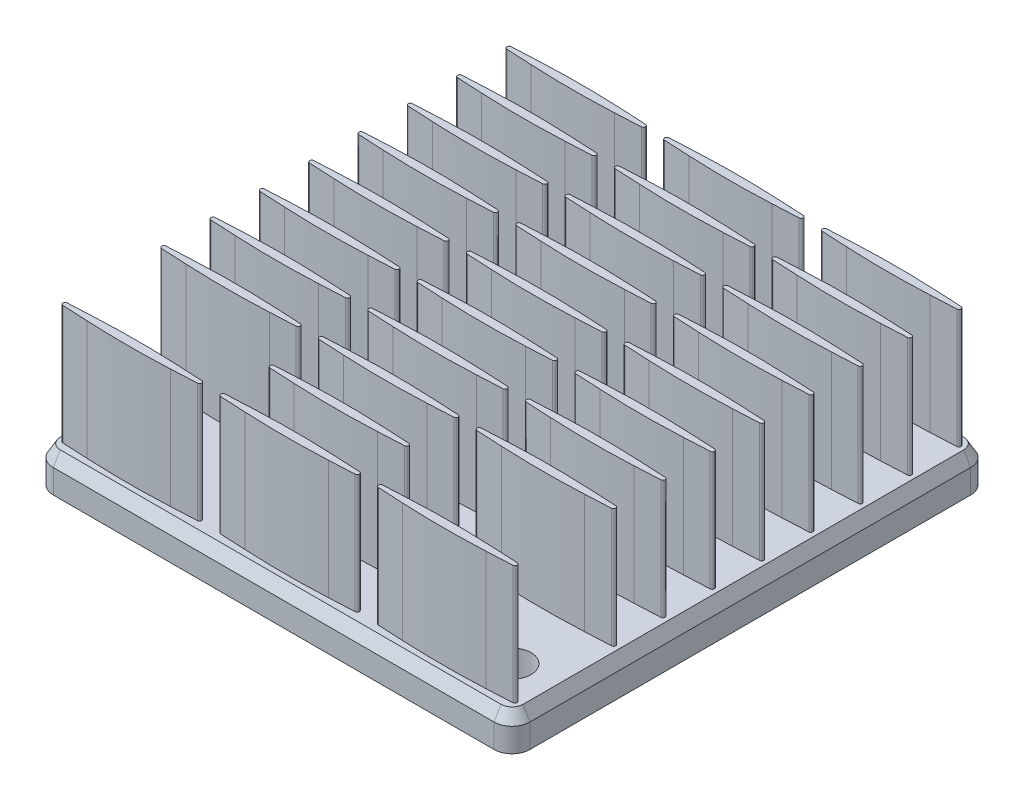
SolidWorks part; units mm, degrees
material "6061 Alloy"
ref_plane "Front Plane" through (0, 0, 0) normal (0, 0, 1) x (1, 0, 0)
ref_plane "Top Plane" through (0, 0, 0) normal (0, 1, 0) x (1, 0, 0)
ref_plane "Right Plane" through (0, 0, 0) normal (1, 0, 0) x (0, 0, -1)
ref_plane "Plane1" through (0, 3, 0) normal (0, 1, 0) x (1, 0, 0)
sketch "Sketch1" plane through (0, 3, 0) normal (0, 1, 0) x (1, 0, 0)
  line L0 (-19.4226, 18.5) -> (-19.4226, -18.5)
  line L1 (-18.5, -19.4226) -> (18.5, -19.4226)
  line L2 (19.4226, -18.5) -> (19.4226, 18.5)
  line L3 (18.5, 19.4226) -> (-18.5, 19.4226)
  arc A0 (-19.4226, -18.5) -> (-18.5, -19.4226) centre (-18.5, -18.5) ccw
  arc A1 (18.5, -19.4226) -> (19.4226, -18.5) centre (18.5, -18.5) ccw
  arc A2 (19.4226, 18.5) -> (18.5, 19.4226) centre (18.5, 18.5) ccw
  arc A3 (-18.5, 19.4226) -> (-19.4226, 18.5) centre (-18.5, 18.5) ccw
extrude "Boss-Extrude1" add sketch "Sketch1" against normal blind 1 draft 30 draft outward yes
sketch "Sketch2" plane through (0, 2, 0) normal (0, -1, 0) x (1, 0, 0)
  line L0 (-20, -18.5) -> (-20, 18.5)
  line L1 (-18.5, 20) -> (18.5, 20)
  line L2 (20, 18.5) -> (20, -18.5)
  line L3 (18.5, -20) -> (-18.5, -20)
  arc A0 (-18.5, -20) -> (-20, -18.5) centre (-18.5, -18.5) cw
  arc A1 (-20, 18.5) -> (-18.5, 20) centre (-18.5, 18.5) cw
  arc A2 (18.5, 20) -> (20, 18.5) centre (18.5, 18.5) cw
  arc A3 (20, -18.5) -> (18.5, -20) centre (18.5, -18.5) cw
extrude "Boss-Extrude2" add sketch "Sketch2" along normal blind 2
sketch "Sketch3" plane through (0, 3, 0) normal (0, 1, 0) x (-1, 0, 0)
  line L0 (-16.7428, -18.9173) -> (-18.889, -18.8098)
  line L1 (-18.889, -18.4502) -> (-16.7428, -18.3427)
  line L2 (-9.7372, -18.3427) -> (-7.591, -18.4502)
  line L3 (-7.591, -18.8098) -> (-9.7372, -18.9173)
  arc A0 (-9.7372, -18.9173) -> (-16.7428, -18.9173) centre (-13.24, 50.995) cw
  arc A1 (-18.889, -18.8098) -> (-18.889, -18.4502) centre (-18.88, -18.63) cw
  arc A2 (-16.7428, -18.3427) -> (-9.7372, -18.3427) centre (-13.24, -88.255) cw
  arc A3 (-7.591, -18.4502) -> (-7.591, -18.8098) centre (-7.6, -18.63) cw
extrude "Boss-Extrude3" add sketch "Sketch3" along normal blind 10
sketch "Sketch4" plane through (0, 3, 0) normal (0, 1, 0) x (-1, 0, 0)
  line L0 (-3.5028, -18.9173) -> (-5.649, -18.8098)
  line L1 (-5.649, -18.4502) -> (-3.5028, -18.3427)
  line L2 (3.5028, -18.3427) -> (5.649, -18.4502)
  line L3 (5.649, -18.8098) -> (3.5028, -18.9173)
  arc A0 (3.5028, -18.9173) -> (-3.5028, -18.9173) centre (0, 50.995) cw
  arc A1 (-5.649, -18.8098) -> (-5.649, -18.4502) centre (-5.64, -18.63) cw
  arc A2 (-3.5028, -18.3427) -> (3.5028, -18.3427) centre (0, -88.255) cw
  arc A3 (5.649, -18.4502) -> (5.649, -18.8098) centre (5.64, -18.63) cw
extrude "Boss-Extrude4" add sketch "Sketch4" along normal blind 12
sketch "Sketch5" plane through (0, 3, 0) normal (0, 1, 0) x (-1, 0, 0)
  line L0 (9.7372, -18.9173) -> (7.591, -18.8098)
  line L1 (7.591, -18.4502) -> (9.7372, -18.3427)
  line L2 (16.7428, -18.3427) -> (18.889, -18.4502)
  line L3 (18.889, -18.8098) -> (16.7428, -18.9173)
  arc A0 (16.7428, -18.9173) -> (9.7372, -18.9173) centre (13.24, 50.995) cw
  arc A1 (7.591, -18.8098) -> (7.591, -18.4502) centre (7.6, -18.63) cw
  arc A2 (9.7372, -18.3427) -> (16.7428, -18.3427) centre (13.24, -88.255) cw
  arc A3 (18.889, -18.4502) -> (18.889, -18.8098) centre (18.88, -18.63) cw
extrude "Boss-Extrude5" add sketch "Sketch5" along normal blind 12
sketch "Sketch6" plane through (0, 3, 0) normal (0, 1, 0) x (-1, 0, 0)
  line L0 (-16.7428, -14.7773) -> (-18.889, -14.6698)
  line L1 (-18.889, -14.3102) -> (-16.7428, -14.2027)
  line L2 (-9.7372, -14.2027) -> (-7.591, -14.3102)
  line L3 (-7.591, -14.6698) -> (-9.7372, -14.7773)
  arc A0 (-9.7372, -14.7773) -> (-16.7428, -14.7773) centre (-13.24, 55.135) cw
  arc A1 (-18.889, -14.6698) -> (-18.889, -14.3102) centre (-18.88, -14.49) cw
  arc A2 (-16.7428, -14.2027) -> (-9.7372, -14.2027) centre (-13.24, -84.115) cw
  arc A3 (-7.591, -14.3102) -> (-7.591, -14.6698) centre (-7.6, -14.49) cw
extrude "Boss-Extrude6" add sketch "Sketch6" along normal blind 12
sketch "Sketch7" plane through (0, 3, 0) normal (0, 1, 0) x (-1, 0, 0)
  line L0 (-3.5028, -14.7773) -> (-5.649, -14.6698)
  line L1 (-5.649, -14.3102) -> (-3.5028, -14.2027)
  line L2 (3.5028, -14.2027) -> (5.649, -14.3102)
  line L3 (5.649, -14.6698) -> (3.5028, -14.7773)
  arc A0 (3.5028, -14.7773) -> (-3.5028, -14.7773) centre (0, 55.135) cw
  arc A1 (-5.649, -14.6698) -> (-5.649, -14.3102) centre (-5.64, -14.49) cw
  arc A2 (-3.5028, -14.2027) -> (3.5028, -14.2027) centre (0, -84.115) cw
  arc A3 (5.649, -14.3102) -> (5.649, -14.6698) centre (5.64, -14.49) cw
extrude "Boss-Extrude7" add sketch "Sketch7" along normal blind 12
sketch "Sketch8" plane through (0, 3, 0) normal (0, 1, 0) x (-1, 0, 0)
  line L0 (9.7372, -14.7773) -> (7.591, -14.6698)
  line L1 (7.591, -14.3102) -> (9.7372, -14.2027)
  line L2 (16.7428, -14.2027) -> (18.889, -14.3102)
  line L3 (18.889, -14.6698) -> (16.7428, -14.7773)
  arc A0 (16.7428, -14.7773) -> (9.7372, -14.7773) centre (13.24, 55.135) cw
  arc A1 (7.591, -14.6698) -> (7.591, -14.3102) centre (7.6, -14.49) cw
  arc A2 (9.7372, -14.2027) -> (16.7428, -14.2027) centre (13.24, -84.115) cw
  arc A3 (18.889, -14.3102) -> (18.889, -14.6698) centre (18.88, -14.49) cw
extrude "Boss-Extrude8" add sketch "Sketch8" along normal blind 12
sketch "Sketch9" plane through (0, 3, 0) normal (0, 1, 0) x (-1, 0, 0)
  line L0 (-16.7428, -10.6373) -> (-18.889, -10.5298)
  line L1 (-18.889, -10.1702) -> (-16.7428, -10.0627)
  line L2 (-9.7372, -10.0627) -> (-7.591, -10.1702)
  line L3 (-7.591, -10.5298) -> (-9.7372, -10.6373)
  arc A0 (-9.7372, -10.6373) -> (-16.7428, -10.6373) centre (-13.24, 59.275) cw
  arc A1 (-18.889, -10.5298) -> (-18.889, -10.1702) centre (-18.88, -10.35) cw
  arc A2 (-16.7428, -10.0627) -> (-9.7372, -10.0627) centre (-13.24, -79.975) cw
  arc A3 (-7.591, -10.1702) -> (-7.591, -10.5298) centre (-7.6, -10.35) cw
extrude "Boss-Extrude9" add sketch "Sketch9" along normal blind 12
sketch "Sketch10" plane through (0, 3, 0) normal (0, 1, 0) x (-1, 0, 0)
  line L0 (-3.5028, -10.6373) -> (-5.649, -10.5298)
  line L1 (-5.649, -10.1702) -> (-3.5028, -10.0627)
  line L2 (3.5028, -10.0627) -> (5.649, -10.1702)
  line L3 (5.649, -10.5298) -> (3.5028, -10.6373)
  arc A0 (3.5028, -10.6373) -> (-3.5028, -10.6373) centre (0, 59.275) cw
  arc A1 (-5.649, -10.5298) -> (-5.649, -10.1702) centre (-5.64, -10.35) cw
  arc A2 (-3.5028, -10.0627) -> (3.5028, -10.0627) centre (0, -79.975) cw
  arc A3 (5.649, -10.1702) -> (5.649, -10.5298) centre (5.64, -10.35) cw
extrude "Boss-Extrude10" add sketch "Sketch10" along normal blind 12
sketch "Sketch11" plane through (0, 3, 0) normal (0, 1, 0) x (-1, 0, 0)
  line L0 (9.7372, -10.6373) -> (7.591, -10.5298)
  line L1 (7.591, -10.1702) -> (9.7372, -10.0627)
  line L2 (16.7428, -10.0627) -> (18.889, -10.1702)
  line L3 (18.889, -10.5298) -> (16.7428, -10.6373)
  arc A0 (16.7428, -10.6373) -> (9.7372, -10.6373) centre (13.24, 59.275) cw
  arc A1 (7.591, -10.5298) -> (7.591, -10.1702) centre (7.6, -10.35) cw
  arc A2 (9.7372, -10.0627) -> (16.7428, -10.0627) centre (13.24, -79.975) cw
  arc A3 (18.889, -10.1702) -> (18.889, -10.5298) centre (18.88, -10.35) cw
extrude "Boss-Extrude11" add sketch "Sketch11" along normal blind 12
sketch "Sketch12" plane through (0, 3, 0) normal (0, 1, 0) x (-1, 0, 0)
  line L0 (-16.7428, -6.4973) -> (-18.889, -6.3898)
  line L1 (-18.889, -6.0302) -> (-16.7428, -5.9227)
  line L2 (-9.7372, -5.9227) -> (-7.591, -6.0302)
  line L3 (-7.591, -6.3898) -> (-9.7372, -6.4973)
  arc A0 (-9.7372, -6.4973) -> (-16.7428, -6.4973) centre (-13.24, 63.415) cw
  arc A1 (-18.889, -6.3898) -> (-18.889, -6.0302) centre (-18.88, -6.21) cw
  arc A2 (-16.7428, -5.9227) -> (-9.7372, -5.9227) centre (-13.24, -75.835) cw
  arc A3 (-7.591, -6.0302) -> (-7.591, -6.3898) centre (-7.6, -6.21) cw
extrude "Boss-Extrude12" add sketch "Sketch12" along normal blind 12
sketch "Sketch13" plane through (0, 3, 0) normal (0, 1, 0) x (-1, 0, 0)
  line L0 (-3.5028, -6.4973) -> (-5.649, -6.3898)
  line L1 (-5.649, -6.0302) -> (-3.5028, -5.9227)
  line L2 (3.5028, -5.9227) -> (5.649, -6.0302)
  line L3 (5.649, -6.3898) -> (3.5028, -6.4973)
  arc A0 (3.5028, -6.4973) -> (-3.5028, -6.4973) centre (0, 63.415) cw
  arc A1 (-5.649, -6.3898) -> (-5.649, -6.0302) centre (-5.64, -6.21) cw
  arc A2 (-3.5028, -5.9227) -> (3.5028, -5.9227) centre (0, -75.835) cw
  arc A3 (5.649, -6.0302) -> (5.649, -6.3898) centre (5.64, -6.21) cw
extrude "Boss-Extrude13" add sketch "Sketch13" along normal blind 12
sketch "Sketch14" plane through (0, 3, 0) normal (0, 1, 0) x (-1, 0, 0)
  line L0 (9.7372, -6.4973) -> (7.591, -6.3898)
  line L1 (7.591, -6.0302) -> (9.7372, -5.9227)
  line L2 (16.7428, -5.9227) -> (18.889, -6.0302)
  line L3 (18.889, -6.3898) -> (16.7428, -6.4973)
  arc A0 (16.7428, -6.4973) -> (9.7372, -6.4973) centre (13.24, 63.415) cw
  arc A1 (7.591, -6.3898) -> (7.591, -6.0302) centre (7.6, -6.21) cw
  arc A2 (9.7372, -5.9227) -> (16.7428, -5.9227) centre (13.24, -75.835) cw
  arc A3 (18.889, -6.0302) -> (18.889, -6.3898) centre (18.88, -6.21) cw
extrude "Boss-Extrude14" add sketch "Sketch14" along normal blind 12
sketch "Sketch15" plane through (0, 3, 0) normal (0, 1, 0) x (-1, 0, 0)
  line L0 (-16.7428, -2.3573) -> (-18.889, -2.2498)
  line L1 (-18.889, -1.8902) -> (-16.7428, -1.7827)
  line L2 (-9.7372, -1.7827) -> (-7.591, -1.8902)
  line L3 (-7.591, -2.2498) -> (-9.7372, -2.3573)
  arc A0 (-9.7372, -2.3573) -> (-16.7428, -2.3573) centre (-13.24, 67.555) cw
  arc A1 (-18.889, -2.2498) -> (-18.889, -1.8902) centre (-18.88, -2.07) cw
  arc A2 (-16.7428, -1.7827) -> (-9.7372, -1.7827) centre (-13.24, -71.695) cw
  arc A3 (-7.591, -1.8902) -> (-7.591, -2.2498) centre (-7.6, -2.07) cw
extrude "Boss-Extrude15" add sketch "Sketch15" along normal blind 12
sketch "Sketch16" plane through (0, 3, 0) normal (0, 1, 0) x (-1, 0, 0)
  line L0 (-3.5028, -2.3573) -> (-5.649, -2.2498)
  line L1 (-5.649, -1.8902) -> (-3.5028, -1.7827)
  line L2 (3.5028, -1.7827) -> (5.649, -1.8902)
  line L3 (5.649, -2.2498) -> (3.5028, -2.3573)
  arc A0 (3.5028, -2.3573) -> (-3.5028, -2.3573) centre (0, 67.555) cw
  arc A1 (-5.649, -2.2498) -> (-5.649, -1.8902) centre (-5.64, -2.07) cw
  arc A2 (-3.5028, -1.7827) -> (3.5028, -1.7827) centre (0, -71.695) cw
  arc A3 (5.649, -1.8902) -> (5.649, -2.2498) centre (5.64, -2.07) cw
extrude "Boss-Extrude16" add sketch "Sketch16" along normal blind 12
sketch "Sketch17" plane through (0, 3, 0) normal (0, 1, 0) x (-1, 0, 0)
  line L0 (9.7372, -2.3573) -> (7.591, -2.2498)
  line L1 (7.591, -1.8902) -> (9.7372, -1.7827)
  line L2 (16.7428, -1.7827) -> (18.889, -1.8902)
  line L3 (18.889, -2.2498) -> (16.7428, -2.3573)
  arc A0 (16.7428, -2.3573) -> (9.7372, -2.3573) centre (13.24, 67.555) cw
  arc A1 (7.591, -2.2498) -> (7.591, -1.8902) centre (7.6, -2.07) cw
  arc A2 (9.7372, -1.7827) -> (16.7428, -1.7827) centre (13.24, -71.695) cw
  arc A3 (18.889, -1.8902) -> (18.889, -2.2498) centre (18.88, -2.07) cw
extrude "Boss-Extrude17" add sketch "Sketch17" along normal blind 12
sketch "Sketch18" plane through (0, 3, 0) normal (0, 1, 0) x (-1, 0, 0)
  line L0 (-16.7428, 1.7827) -> (-18.889, 1.8902)
  line L1 (-18.889, 2.2498) -> (-16.7428, 2.3573)
  line L2 (-9.7372, 2.3573) -> (-7.591, 2.2498)
  line L3 (-7.591, 1.8902) -> (-9.7372, 1.7827)
  arc A0 (-9.7372, 1.7827) -> (-16.7428, 1.7827) centre (-13.24, 71.695) cw
  arc A1 (-18.889, 1.8902) -> (-18.889, 2.2498) centre (-18.88, 2.07) cw
  arc A2 (-16.7428, 2.3573) -> (-9.7372, 2.3573) centre (-13.24, -67.555) cw
  arc A3 (-7.591, 2.2498) -> (-7.591, 1.8902) centre (-7.6, 2.07) cw
extrude "Boss-Extrude18" add sketch "Sketch18" along normal blind 12
sketch "Sketch19" plane through (0, 3, 0) normal (0, 1, 0) x (-1, 0, 0)
  line L0 (-3.5028, 1.7827) -> (-5.649, 1.8902)
  line L1 (-5.649, 2.2498) -> (-3.5028, 2.3573)
  line L2 (3.5028, 2.3573) -> (5.649, 2.2498)
  line L3 (5.649, 1.8902) -> (3.5028, 1.7827)
  arc A0 (3.5028, 1.7827) -> (-3.5028, 1.7827) centre (0, 71.695) cw
  arc A1 (-5.649, 1.8902) -> (-5.649, 2.2498) centre (-5.64, 2.07) cw
  arc A2 (-3.5028, 2.3573) -> (3.5028, 2.3573) centre (0, -67.555) cw
  arc A3 (5.649, 2.2498) -> (5.649, 1.8902) centre (5.64, 2.07) cw
extrude "Boss-Extrude19" add sketch "Sketch19" along normal blind 12
sketch "Sketch20" plane through (0, 3, 0) normal (0, 1, 0) x (-1, 0, 0)
  line L0 (9.7372, 1.7827) -> (7.591, 1.8902)
  line L1 (7.591, 2.2498) -> (9.7372, 2.3573)
  line L2 (16.7428, 2.3573) -> (18.889, 2.2498)
  line L3 (18.889, 1.8902) -> (16.7428, 1.7827)
  arc A0 (16.7428, 1.7827) -> (9.7372, 1.7827) centre (13.24, 71.695) cw
  arc A1 (7.591, 1.8902) -> (7.591, 2.2498) centre (7.6, 2.07) cw
  arc A2 (9.7372, 2.3573) -> (16.7428, 2.3573) centre (13.24, -67.555) cw
  arc A3 (18.889, 2.2498) -> (18.889, 1.8902) centre (18.88, 2.07) cw
extrude "Boss-Extrude20" add sketch "Sketch20" along normal blind 12
sketch "Sketch21" plane through (0, 3, 0) normal (0, 1, 0) x (-1, 0, 0)
  line L0 (-16.7428, 5.9227) -> (-18.889, 6.0302)
  line L1 (-18.889, 6.3898) -> (-16.7428, 6.4973)
  line L2 (-9.7372, 6.4973) -> (-7.591, 6.3898)
  line L3 (-7.591, 6.0302) -> (-9.7372, 5.9227)
  arc A0 (-9.7372, 5.9227) -> (-16.7428, 5.9227) centre (-13.24, 75.835) cw
  arc A1 (-18.889, 6.0302) -> (-18.889, 6.3898) centre (-18.88, 6.21) cw
  arc A2 (-16.7428, 6.4973) -> (-9.7372, 6.4973) centre (-13.24, -63.415) cw
  arc A3 (-7.591, 6.3898) -> (-7.591, 6.0302) centre (-7.6, 6.21) cw
extrude "Boss-Extrude21" add sketch "Sketch21" along normal blind 12
sketch "Sketch22" plane through (0, 3, 0) normal (0, 1, 0) x (-1, 0, 0)
  line L0 (-3.5028, 5.9227) -> (-5.649, 6.0302)
  line L1 (-5.649, 6.3898) -> (-3.5028, 6.4973)
  line L2 (3.5028, 6.4973) -> (5.649, 6.3898)
  line L3 (5.649, 6.0302) -> (3.5028, 5.9227)
  arc A0 (3.5028, 5.9227) -> (-3.5028, 5.9227) centre (0, 75.835) cw
  arc A1 (-5.649, 6.0302) -> (-5.649, 6.3898) centre (-5.64, 6.21) cw
  arc A2 (-3.5028, 6.4973) -> (3.5028, 6.4973) centre (0, -63.415) cw
  arc A3 (5.649, 6.3898) -> (5.649, 6.0302) centre (5.64, 6.21) cw
extrude "Boss-Extrude22" add sketch "Sketch22" along normal blind 12
sketch "Sketch23" plane through (0, 3, 0) normal (0, 1, 0) x (-1, 0, 0)
  line L0 (9.7372, 5.9227) -> (7.591, 6.0302)
  line L1 (7.591, 6.3898) -> (9.7372, 6.4973)
  line L2 (16.7428, 6.4973) -> (18.889, 6.3898)
  line L3 (18.889, 6.0302) -> (16.7428, 5.9227)
  arc A0 (16.7428, 5.9227) -> (9.7372, 5.9227) centre (13.24, 75.835) cw
  arc A1 (7.591, 6.0302) -> (7.591, 6.3898) centre (7.6, 6.21) cw
  arc A2 (9.7372, 6.4973) -> (16.7428, 6.4973) centre (13.24, -63.415) cw
  arc A3 (18.889, 6.3898) -> (18.889, 6.0302) centre (18.88, 6.21) cw
extrude "Boss-Extrude23" add sketch "Sketch23" along normal blind 12
sketch "Sketch24" plane through (0, 3, 0) normal (0, 1, 0) x (-1, 0, 0)
  line L0 (-16.7428, 10.0627) -> (-18.889, 10.1702)
  line L1 (-18.889, 10.5298) -> (-16.7428, 10.6373)
  line L2 (-9.7372, 10.6373) -> (-7.591, 10.5298)
  line L3 (-7.591, 10.1702) -> (-9.7372, 10.0627)
  arc A0 (-9.7372, 10.0627) -> (-16.7428, 10.0627) centre (-13.24, 79.975) cw
  arc A1 (-18.889, 10.1702) -> (-18.889, 10.5298) centre (-18.88, 10.35) cw
  arc A2 (-16.7428, 10.6373) -> (-9.7372, 10.6373) centre (-13.24, -59.275) cw
  arc A3 (-7.591, 10.5298) -> (-7.591, 10.1702) centre (-7.6, 10.35) cw
extrude "Boss-Extrude24" add sketch "Sketch24" along normal blind 12
sketch "Sketch25" plane through (0, 3, 0) normal (0, 1, 0) x (-1, 0, 0)
  line L0 (-3.5028, 10.0627) -> (-5.649, 10.1702)
  line L1 (-5.649, 10.5298) -> (-3.5028, 10.6373)
  line L2 (3.5028, 10.6373) -> (5.649, 10.5298)
  line L3 (5.649, 10.1702) -> (3.5028, 10.0627)
  arc A0 (3.5028, 10.0627) -> (-3.5028, 10.0627) centre (0, 79.975) cw
  arc A1 (-5.649, 10.1702) -> (-5.649, 10.5298) centre (-5.64, 10.35) cw
  arc A2 (-3.5028, 10.6373) -> (3.5028, 10.6373) centre (0, -59.275) cw
  arc A3 (5.649, 10.5298) -> (5.649, 10.1702) centre (5.64, 10.35) cw
extrude "Boss-Extrude25" add sketch "Sketch25" along normal blind 12
sketch "Sketch26" plane through (0, 3, 0) normal (0, 1, 0) x (-1, 0, 0)
  line L0 (9.7372, 10.0627) -> (7.591, 10.1702)
  line L1 (7.591, 10.5298) -> (9.7372, 10.6373)
  line L2 (16.7428, 10.6373) -> (18.889, 10.5298)
  line L3 (18.889, 10.1702) -> (16.7428, 10.0627)
  arc A0 (16.7428, 10.0627) -> (9.7372, 10.0627) centre (13.24, 79.975) cw
  arc A1 (7.591, 10.1702) -> (7.591, 10.5298) centre (7.6, 10.35) cw
  arc A2 (9.7372, 10.6373) -> (16.7428, 10.6373) centre (13.24, -59.275) cw
  arc A3 (18.889, 10.5298) -> (18.889, 10.1702) centre (18.88, 10.35) cw
extrude "Boss-Extrude26" add sketch "Sketch26" along normal blind 12
sketch "Sketch28" plane through (0, 3, 0) normal (0, 1, 0) x (-1, 0, 0)
  line L0 (-3.5028, 14.2027) -> (-5.649, 14.3102)
  line L1 (-5.649, 14.6698) -> (-3.5028, 14.7773)
  line L2 (3.5028, 14.7773) -> (5.649, 14.6698)
  line L3 (5.649, 14.3102) -> (3.5028, 14.2027)
  arc A0 (3.5028, 14.2027) -> (-3.5028, 14.2027) centre (0, 84.115) cw
  arc A1 (-5.649, 14.3102) -> (-5.649, 14.6698) centre (-5.64, 14.49) cw
  arc A2 (-3.5028, 14.7773) -> (3.5028, 14.7773) centre (0, -55.135) cw
  arc A3 (5.649, 14.6698) -> (5.649, 14.3102) centre (5.64, 14.49) cw
extrude "Boss-Extrude28" add sketch "Sketch28" along normal blind 12
sketch "Sketch30" plane through (0, 3, 0) normal (0, 1, 0) x (-1, 0, 0)
  line L0 (-16.7428, 18.3427) -> (-18.889, 18.4502)
  line L1 (-18.889, 18.8098) -> (-16.7428, 18.9173)
  line L2 (-9.7372, 18.9173) -> (-7.591, 18.8098)
  line L3 (-7.591, 18.4502) -> (-9.7372, 18.3427)
  arc A0 (-9.7372, 18.3427) -> (-16.7428, 18.3427) centre (-13.24, 88.255) cw
  arc A1 (-18.889, 18.4502) -> (-18.889, 18.8098) centre (-18.88, 18.63) cw
  arc A2 (-16.7428, 18.9173) -> (-9.7372, 18.9173) centre (-13.24, -50.995) cw
  arc A3 (-7.591, 18.8098) -> (-7.591, 18.4502) centre (-7.6, 18.63) cw
extrude "Boss-Extrude30" add sketch "Sketch30" along normal blind 12
sketch "Sketch31" plane through (0, 3, 0) normal (0, 1, 0) x (-1, 0, 0)
  line L0 (-3.5028, 18.3427) -> (-5.649, 18.4502)
  line L1 (-5.649, 18.8098) -> (-3.5028, 18.9173)
  line L2 (3.5028, 18.9173) -> (5.649, 18.8098)
  line L3 (5.649, 18.4502) -> (3.5028, 18.3427)
  arc A0 (3.5028, 18.3427) -> (-3.5028, 18.3427) centre (0, 88.255) cw
  arc A1 (-5.649, 18.4502) -> (-5.649, 18.8098) centre (-5.64, 18.63) cw
  arc A2 (-3.5028, 18.9173) -> (3.5028, 18.9173) centre (0, -50.995) cw
  arc A3 (5.649, 18.8098) -> (5.649, 18.4502) centre (5.64, 18.63) cw
extrude "Boss-Extrude31" add sketch "Sketch31" along normal blind 12
sketch "Sketch32" plane through (0, 3, 0) normal (0, 1, 0) x (-1, 0, 0)
  line L0 (9.7372, 18.3427) -> (7.591, 18.4502)
  line L1 (7.591, 18.8098) -> (9.7372, 18.9173)
  line L2 (16.7428, 18.9173) -> (18.889, 18.8098)
  line L3 (18.889, 18.4502) -> (16.7428, 18.3427)
  arc A0 (16.7428, 18.3427) -> (9.7372, 18.3427) centre (13.24, 88.255) cw
  arc A1 (7.591, 18.4502) -> (7.591, 18.8098) centre (7.6, 18.63) cw
  arc A2 (9.7372, 18.9173) -> (16.7428, 18.9173) centre (13.24, -50.995) cw
  arc A3 (18.889, 18.8098) -> (18.889, 18.4502) centre (18.88, 18.63) cw
extrude "Boss-Extrude32" add sketch "Sketch32" along normal blind 12
sketch "Sketch34" plane through (0, 15, 0) normal (0, 1, 0) x (1, 0, 0)
  line L1 (-25.0282, 24.7256) -> (32.2518, 24.7256)
  line L2 (-25.0282, 24.7256) -> (-25.0282, -28.902)
  line L3 (-25.0282, -28.902) -> (32.2518, -28.902)
  line L4 (32.2518, 24.7256) -> (32.2518, -28.902)
extrude "Cut-Extrude1" cut sketch "Sketch34" against normal blind 2
sketch "Sketch35" plane through (0, 0, 0) normal (0, -1, 0) x (1, 0, 0)
  circle A0 centre (16, 16) radius 1.6
  circle A1 centre (-16, 16) radius 1.6
  dimension "D1" = 3.2
  dimension "D2" = 32
  dimension "D3" = 16
  dimension "D4" = 16
extrude "Cut-Extrude2" cut sketch "Sketch35" against normal blind 10
